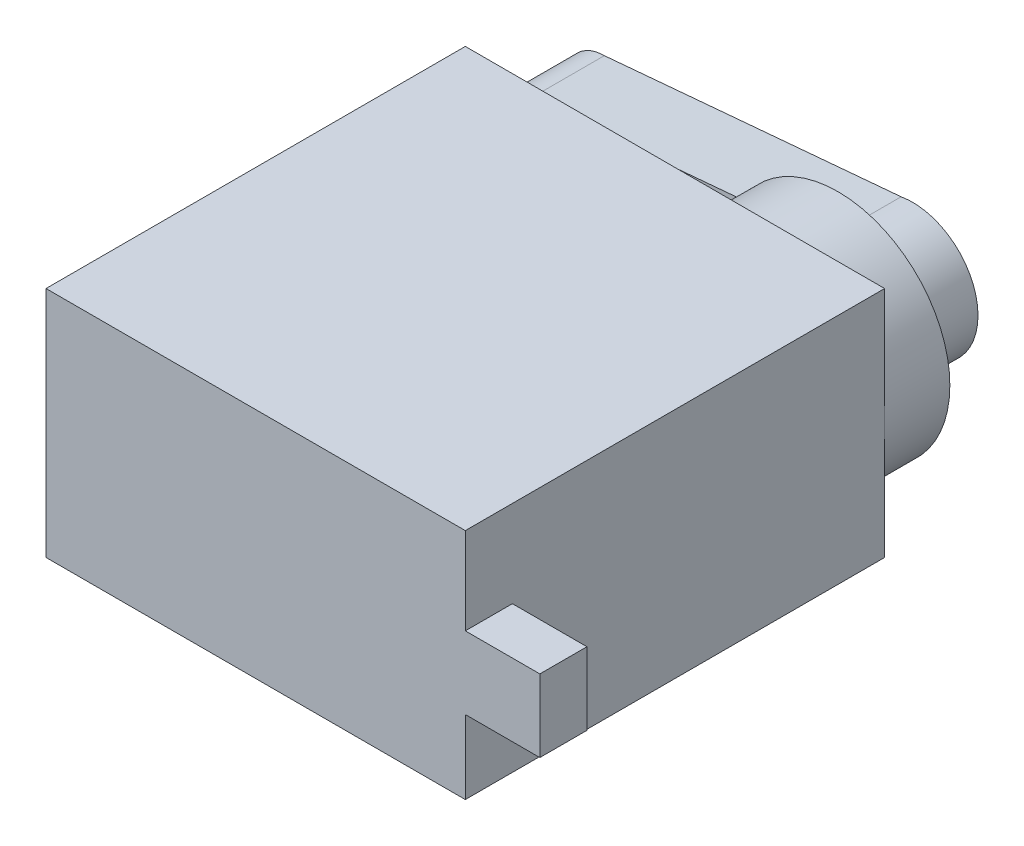
SolidWorks part; units mm, degrees
ref_plane "Front Plane" through (0, 0, 0) normal (0, 0, 1) x (1, 0, 0)
ref_plane "Top Plane" through (0, 0, 0) normal (0, 1, 0) x (1, 0, 0)
ref_plane "Right Plane" through (0, 0, 0) normal (1, 0, 0) x (0, 0, -1)
sketch "Sketch1" plane through (0, 0, 0) normal (0, 0, 1) x (1, 0, 0)
  line L1 (-11.25, 6.25) -> (11.25, 6.25)
  line L2 (-11.25, 6.25) -> (-11.25, -6.25)
  line L3 (-11.25, -6.25) -> (11.25, -6.25)
  line L4 (11.25, 6.25) -> (11.25, -6.25)
  line L5 (-11.25, 6.25) -> (11.25, -6.25) construction
  line L6 (-11.25, -6.25) -> (11.25, 6.25) construction
  point P0 (0, 0)
  dimension "D1" = 22.5
  dimension "D2" = 12.5
extrude "Boss-Extrude1" add sketch "Sketch1" along normal blind 22.5
sketch "Sketch2" plane through (0, 0, 0) normal (0, 0, -1) x (-1, 0, 0)
  line L0 (-11.25, 0) -> (-5.25, 0)
  line L1 (-11.25, -6.25) -> (-11.25, 6.25) construction
  circle A0 centre (-5.25, 0) radius 6
extrude "Boss-Extrude2" add sketch "Sketch2" along normal blind 3.5
sketch "Sketch5" plane through (0, 0, -3.5) normal (0, 0, -1) x (-1, 0, 0)
  line L1 (-4.6351, 3.4557) -> (11.29, 2.05)
  line L3 (11.29, -2.05) -> (-4.6351, -3.4557)
  arc A0 (-4.6351, 3.4557) -> (-4.6351, -3.4557) centre (-5.25, 0) ccw
  arc A1 (11.29, -2.05) -> (11.29, 2.05) centre (11.29, 0) ccw
extrude "Boss-Extrude4" add sketch "Sketch5" along normal blind 4
sketch "Sketch6" plane through (11.25, 0, 0) normal (1, 0, 0) x (0, 0, -1)
  line L0 (-22.5, -6.25) -> (-22.5, 6.25) construction
  line L1 (-22.5, 1.5907) -> (-19.9739, 1.5907)
  line L2 (-22.5, 1.5907) -> (-22.5, -2.2973)
  line L3 (-22.5, -2.2973) -> (-19.9739, -2.2973)
  line L4 (-19.9739, 1.5907) -> (-19.9739, -2.2973)
extrude "Boss-Extrude5" add sketch "Sketch6" along normal blind 4
